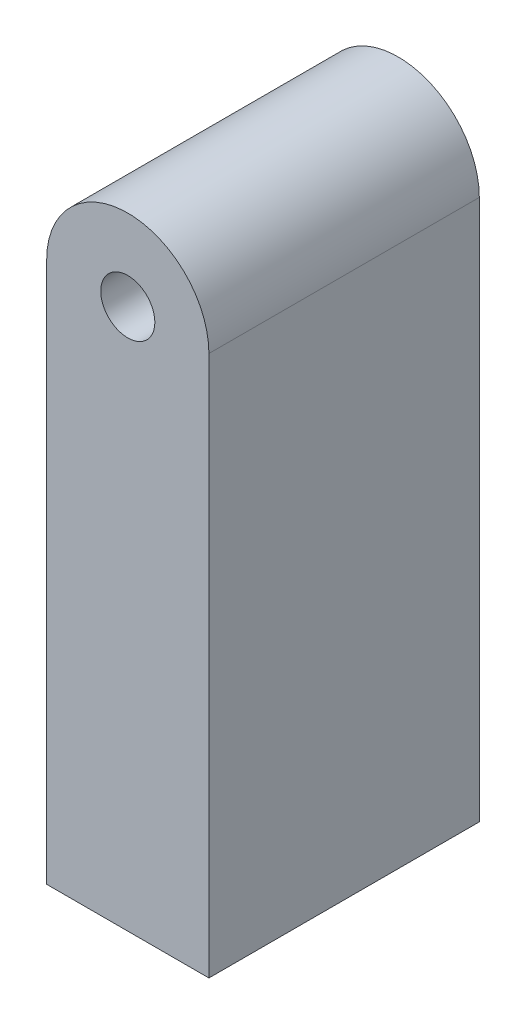
SolidWorks part; units mm, degrees
ref_plane "Front Plane" through (0, 0, 0) normal (0, 0, 1) x (1, 0, 0)
ref_plane "Top Plane" through (0, 0, 0) normal (0, 1, 0) x (1, 0, 0)
ref_plane "Right Plane" through (0, 0, 0) normal (1, 0, 0) x (0, 0, -1)
sketch "Sketch2" plane through (0, 0, 0) normal (0, 0, 1) x (1, 0, 0)
  line L1 (-0.381, -1.27) -> (0.381, -1.27)
  line L2 (-0.381, -1.27) -> (-0.381, 1.27)
  line L3 (-0.381, 1.27) -> (0.381, 1.27)
  line L4 (0.381, -1.27) -> (0.381, 1.27)
  line L5 (-0.381, -1.27) -> (0.381, 1.27) construction
  line L6 (-0.381, 1.27) -> (0.381, -1.27) construction
  circle A0 centre (0, 1.27) radius 0.381
  circle A1 centre (0, 1.27) radius 0.127
  point P0 (0, 0)
  dimension "D3" = 0.254
  dimension "D1" = 2.54
  dimension "D2" = 0.762
extrude "Boss-Extrude1" add sketch "Sketch2" along normal blind 1.27 contours A1 L3 A0 | A1 L3 A0 | A0 L2 L1 L4
